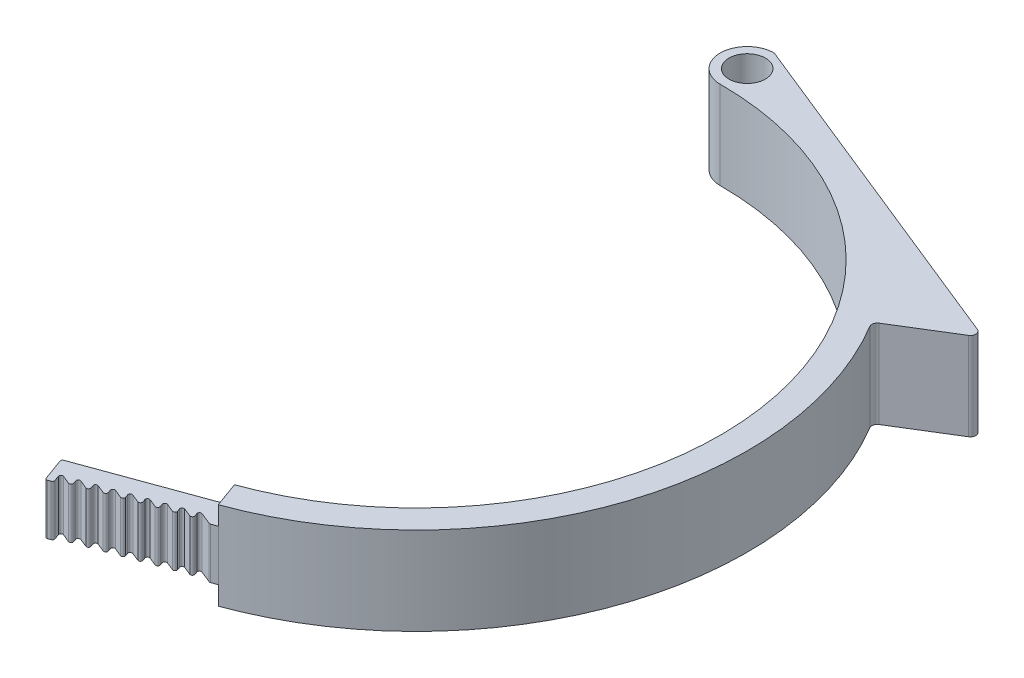
SolidWorks part; units mm, degrees
ref_plane "Front Plane" through (0, 0, 0) normal (0, 0, 1) x (1, 0, 0)
ref_plane "Top Plane" through (0, 0, 0) normal (0, 1, 0) x (1, 0, 0)
ref_plane "Right Plane" through (0, 0, 0) normal (1, 0, 0) x (0, 0, -1)
sketch "Sketch1" plane through (0, 0, 0) normal (0, 1, 0) x (1, 0, 0)
  line L0 (0, 0) -> (15.3909, -42.2862) construction
  line L1 (0, 0) -> (0, -45) construction
  line L2 (0, 0) -> (28.3852, -77.9878) construction
  line L3 (0, 53) -> (51.921, 32.0189)
  line L4 (51.921, 32.0189) -> (41.707, 25.7201)
  line L5 (0, 53) -> (0, 49)
  line L7 (0, 49) -> (0, 53)
  line L8 (15.3909, -42.2862) -> (-3.4029, -49.1266)
  line L9 (-3.4029, -49.1266) -> (-2.0349, -52.8853)
  line L10 (-2.0349, -52.8853) -> (16.759, -46.0449)
  circle A0 centre (0, 0) radius 45 construction
  arc A1 (0, 45) -> (15.3909, -42.2862) centre (0, 0) cw
  arc A2 (0, 45) -> (0, 53) centre (0, 49) cw
  arc A4 (16.759, -46.0449) -> (0, 49) centre (0, 0) ccw
  circle A5 centre (0, 49) radius 2.7
  arc A6 (41.707, 25.7201) -> (0, 49) centre (0, 0) ccw
  point P9 (-2.7189, -51.006)
  point P14 (0.5769, -51.9347)
  dimension "D1" = 90
  dimension "D5" = 56
  dimension "D6" = 5.4
  dimension "D2" = 20
  dimension "D3" = 8
  dimension "D4" = 4
  dimension "D7" = 12
  dimension "D8" = 20
extrude "Boss-Extrude1" add sketch "Sketch1" along normal blind 13
sketch "Sketch2" plane through (0, 13, 0) normal (0, 1, 0) x (1, 0, 0)
  line L0 (-1.0952, -52.5433) -> (-1.7108, -50.8519)
  line L1 (-2.0349, -52.8853) -> (16.759, -46.0449) construction
  line L2 (-1.7108, -50.8519) -> (0.7842, -51.8593)
  line L3 (0.7842, -51.8593) -> (-1.0952, -52.5433)
  line L4 (-3.4029, -49.1266) -> (-2.0349, -52.8853) construction
  line L5 (0.7842, -51.8593) -> (0.1686, -50.1678)
  line L6 (0.1686, -50.1678) -> (2.6636, -51.1752)
  line L7 (2.6636, -51.1752) -> (0.7842, -51.8593)
  line L8 (2.6636, -51.1752) -> (2.048, -49.4838)
  line L9 (2.048, -49.4838) -> (4.543, -50.4912)
  line L10 (4.543, -50.4912) -> (2.6636, -51.1752)
  line L11 (4.543, -50.4912) -> (3.9273, -48.7998)
  line L12 (3.9273, -48.7998) -> (6.4224, -49.8072)
  line L13 (6.4224, -49.8072) -> (4.543, -50.4912)
  line L14 (6.4224, -49.8072) -> (5.8067, -48.1157)
  line L15 (5.8067, -48.1157) -> (8.3018, -49.1231)
  line L16 (8.3018, -49.1231) -> (6.4224, -49.8072)
  line L17 (8.3018, -49.1231) -> (7.6861, -47.4317)
  line L18 (7.6861, -47.4317) -> (10.1811, -48.4391)
  line L19 (10.1811, -48.4391) -> (8.3018, -49.1231)
  line L20 (10.1811, -48.4391) -> (9.5655, -46.7476)
  line L21 (9.5655, -46.7476) -> (12.0605, -47.755)
  line L22 (12.0605, -47.755) -> (10.1811, -48.4391)
  line L23 (12.0605, -47.755) -> (11.4449, -46.0636)
  line L24 (11.4449, -46.0636) -> (13.9399, -47.071)
  line L25 (13.9399, -47.071) -> (12.0605, -47.755)
  line L26 (13.9399, -47.071) -> (13.3243, -45.3796)
  line L27 (13.3243, -45.3796) -> (15.8193, -46.387)
  line L28 (15.8193, -46.387) -> (13.9399, -47.071)
  line L29 (-1.0952, -52.5433) -> (0.7842, -51.8593) construction
  line M10 (-2.0349, -52.8853) -> (16.759, -46.0449)
  dimension "D1" = 1.8
  dimension "D2" = 2
  dimension "D3" = 1
  dimension "D5" = 2
  dimension "D4" = 9
extrude "Cut-Extrude1" cut sketch "Sketch2" against normal blind 20 contours L2 L0 M10 | L6 L5 M10 | L9 L8 M10 | L12 L11 M10 | L15 L14 M10 | L18 L17 M10 | L21 L20 M10 | L24 L23 M10 | L27 L26 M10
fillet "Fillet2" radius 0.3 21 edges at (-3.4029, 6.5, 49.1266) (-2.0349, 6.5, 52.8853) (-1.0952, 6.5, 52.5433) (15.8193, 6.5, 46.387) (13.3243, 6.5, 45.3796) (13.9399, 6.5, 47.071) (11.4449, 6.5, 46.0636) (12.0605, 6.5, 47.755) (9.5655, 6.5, 46.7476) (10.1811, 6.5, 48.4391) (7.6861, 6.5, 47.4317) (8.3018, 6.5, 49.1231) (5.8067, 6.5, 48.1157) (6.4224, 6.5, 49.8072) (3.9273, 6.5, 48.7998) (4.543, 6.5, 50.4912) (2.048, 6.5, 49.4838) (2.6636, 6.5, 51.1752) (0.1686, 6.5, 50.1678) (0.7842, 6.5, 51.8593) (-1.7108, 6.5, 50.8519)
fillet "Fillet1" radius 0.8 3 edges at (0, 6.5, -53) (51.921, 6.5, -32.0189) (41.707, 6.5, -25.7201)
sketch "Sketch3" plane through (-18.7939, 0, 6.8404) normal (-0.9397, 0, 0.342) x (0.342, 0, 0.9397)
  line L0 (45.3, 13) -> (48.7, 13) construction
  line L1 (44.1864, 10.25) -> (50.0968, 10.25)
  line L2 (44.1864, 10.25) -> (44.1864, 2.75)
  line L3 (44.1864, 2.75) -> (50.0968, 2.75)
  line L4 (50.0968, 10.25) -> (50.0968, 2.75)
  dimension "D1" = 7.5
  dimension "D2" = 2.75
extrude "Cut-Extrude2" cut sketch "Sketch3" against normal blind 20 flip side to cut
